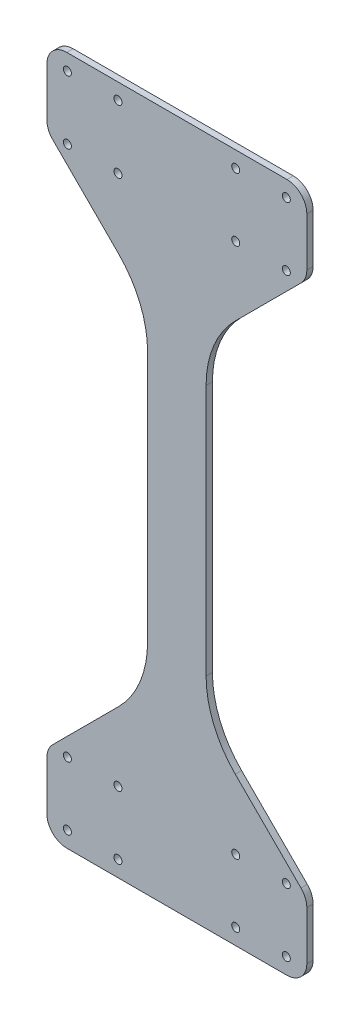
SolidWorks part; units mm, degrees
ref_plane "Front Plane" through (0, 0, 0) normal (0, 0, 1) x (1, 0, 0)
ref_plane "Top Plane" through (0, 0, 0) normal (0, 1, 0) x (1, 0, 0)
ref_plane "Right Plane" through (0, 0, 0) normal (1, 0, 0) x (0, 0, -1)
sketch "Sketch1" plane through (0, 0, 0) normal (0, 0, 1) x (1, 0, 0)
  line L0 (39.3854, -40.0501) -> (39.3854, -52.4111) construction
  line L1 (165.9345, -56.675) -> (165.9345, -42.05) construction
  line L2 (157.3152, -8.05) -> (165.9345, -16.6693)
  line L3 (157.3152, 245.3495) -> (165.9345, 253.9688)
  line L4 (39.3854, -40.0501) -> (39.3854, -52.4111)
  line L5 (165.9345, -56.675) -> (165.9345, -42.05)
  line L6 (165.9345, 245.3495) -> (39.3854, 245.3495)
  line L7 (165.9345, 279.3495) -> (165.9345, 245.3495)
  line L8 (39.3854, -52.4111) -> (165.9345, -56.675)
  line L9 (39.3854, 289.7105) -> (165.9345, 293.9745)
  line L10 (39.3854, -40.0501) -> (39.3854, -16.6693)
  line L11 (165.9345, -42.05) -> (165.9345, -16.6693)
  line L12 (157.3152, -8.05) -> (48.0047, -8.0501)
  line L13 (42.1433, 0) -> (42.1433, 237.2995) construction
  line L14 (42.1433, 118.6497) -> (215.0534, 118.6497) construction
  line L15 (165.9345, 293.9745) -> (165.9345, 279.3495)
  line L16 (39.3854, 277.3495) -> (39.3854, 245.3495)
  line L17 (39.3854, 277.3495) -> (39.3854, 289.7105)
  line L18 (102.66, -54.5431) -> (102.66, 291.8425) construction
  line L19 (102.66, 291.8425) -> (73.0854, -499321.8282) construction
  line L20 (39.3854, -16.6693) -> (89.96, 33.9052)
  line L21 (89.96, -8.05) -> (115.36, -8.05)
  line L22 (89.96, -8.05) -> (89.96, 245.3495)
  line L23 (89.96, 245.3495) -> (115.36, 245.3495)
  line L24 (115.36, -8.05) -> (115.36, 245.3495)
  line L25 (89.96, -8.05) -> (115.36, 245.3495) construction
  line L26 (89.96, 245.3495) -> (115.36, -8.05) construction
  line L27 (115.36, 33.9052) -> (157.3152, -8.05)
  line L28 (115.36, 203.3943) -> (157.3152, 245.3495)
  line L29 (39.3854, 253.9688) -> (89.96, 203.3943)
  arc A0 (157.6345, 249.9303) -> (157.6345, 253.9689) centre (157.6345, 251.9496) cw
  arc A1 (157.6345, 253.9689) -> (157.6345, 249.9303) centre (157.6345, 251.9496) cw
  arc A2 (73.0854, 249.9303) -> (73.0854, 253.9689) centre (73.0854, 251.9496) ccw
  arc A3 (73.0854, 253.9689) -> (73.0854, 249.9303) centre (73.0854, 251.9496) ccw
  arc A4 (73.0854, 249.9303) -> (73.0854, 253.9689) centre (73.0854, 251.9496) ccw
  arc A5 (73.0854, 253.9689) -> (73.0854, 249.9303) centre (73.0854, 251.9496) ccw
  arc A6 (47.6854, 249.9303) -> (47.6854, 253.9689) centre (47.6854, 251.9496) cw
  arc A7 (47.6854, 253.9689) -> (47.6854, 249.9303) centre (47.6854, 251.9496) cw
  arc A10 (47.6854, 281.6802) -> (47.6854, 285.7188) centre (47.6854, 283.6995) cw
  arc A11 (47.6854, 285.7188) -> (47.6854, 281.6802) centre (47.6854, 283.6995) cw
  arc A14 (157.6345, -48.4194) -> (157.6345, -44.3807) centre (157.6345, -46.4001) ccw
  arc A15 (157.6345, -44.3807) -> (157.6345, -48.4194) centre (157.6345, -46.4001) ccw
  arc A16 (157.6345, -48.4194) -> (157.6345, -44.3807) centre (157.6345, -46.4001) ccw
  arc A17 (157.6345, -44.3807) -> (157.6345, -48.4194) centre (157.6345, -46.4001) ccw
  arc A18 (73.0854, 281.6802) -> (73.0854, 285.7188) centre (73.0854, 283.6995) cw
  arc A19 (73.0854, 285.7188) -> (73.0854, 281.6802) centre (73.0854, 283.6995) cw
  arc A22 (157.6345, -16.6693) -> (157.6345, -12.6307) centre (157.6345, -14.65) ccw
  arc A23 (157.6345, -12.6307) -> (157.6345, -16.6693) centre (157.6345, -14.65) ccw
  arc A24 (157.6345, -16.6693) -> (157.6345, -12.6307) centre (157.6345, -14.65) ccw
  arc A25 (157.6345, -12.6307) -> (157.6345, -16.6693) centre (157.6345, -14.65) ccw
  arc A26 (73.0854, -16.6693) -> (73.0854, -12.6307) centre (73.0854, -14.65) ccw
  arc A27 (73.0854, -12.6307) -> (73.0854, -16.6693) centre (73.0854, -14.65) ccw
  arc A28 (73.0854, -16.6693) -> (73.0854, -12.6307) centre (73.0854, -14.65) ccw
  arc A29 (73.0854, -12.6307) -> (73.0854, -16.6693) centre (73.0854, -14.65) ccw
  arc A30 (73.0854, 249.9303) -> (73.0854, 253.9689) centre (73.0854, 251.9496) cw
  arc A31 (73.0854, 253.9689) -> (73.0854, 249.9303) centre (73.0854, 251.9496) cw
  arc A34 (157.6345, 249.9303) -> (157.6345, 253.9689) centre (157.6345, 251.9496) ccw
  arc A35 (157.6345, 253.9689) -> (157.6345, 249.9303) centre (157.6345, 251.9496) ccw
  arc A36 (157.6345, 249.9303) -> (157.6345, 253.9689) centre (157.6345, 251.9496) ccw
  arc A37 (157.6345, 253.9689) -> (157.6345, 249.9303) centre (157.6345, 251.9496) ccw
  arc A38 (47.6854, 249.9303) -> (47.6854, 253.9689) centre (47.6854, 251.9496) ccw
  arc A39 (47.6854, 253.9689) -> (47.6854, 249.9303) centre (47.6854, 251.9496) ccw
  arc A40 (47.6854, 249.9303) -> (47.6854, 253.9689) centre (47.6854, 251.9496) ccw
  arc A41 (47.6854, 253.9689) -> (47.6854, 249.9303) centre (47.6854, 251.9496) ccw
  arc A42 (73.0854, -48.4194) -> (73.0854, -44.3807) centre (73.0854, -46.4001) ccw
  arc A43 (73.0854, -44.3807) -> (73.0854, -48.4194) centre (73.0854, -46.4001) ccw
  arc A44 (73.0854, -48.4194) -> (73.0854, -44.3807) centre (73.0854, -46.4001) ccw
  arc A45 (73.0854, -44.3807) -> (73.0854, -48.4194) centre (73.0854, -46.4001) ccw
  arc A46 (132.2345, 249.9303) -> (132.2345, 253.9689) centre (132.2345, 251.9496) ccw
  arc A47 (132.2345, 253.9689) -> (132.2345, 249.9303) centre (132.2345, 251.9496) ccw
  arc A48 (132.2345, 249.9303) -> (132.2345, 253.9689) centre (132.2345, 251.9496) ccw
  arc A49 (132.2345, 253.9689) -> (132.2345, 249.9303) centre (132.2345, 251.9496) ccw
  arc A50 (47.6854, -48.4194) -> (47.6854, -44.3808) centre (47.6854, -46.4001) ccw
  arc A51 (47.6854, -44.3808) -> (47.6854, -48.4194) centre (47.6854, -46.4001) ccw
  arc A52 (47.6854, -48.4194) -> (47.6854, -44.3808) centre (47.6854, -46.4001) ccw
  arc A53 (47.6854, -44.3808) -> (47.6854, -48.4194) centre (47.6854, -46.4001) ccw
  arc A54 (47.6854, -16.6693) -> (47.6854, -12.6307) centre (47.6854, -14.65) ccw
  arc A55 (47.6854, -12.6307) -> (47.6854, -16.6693) centre (47.6854, -14.65) ccw
  arc A56 (47.6854, -16.6693) -> (47.6854, -12.6307) centre (47.6854, -14.65) ccw
  arc A57 (47.6854, -12.6307) -> (47.6854, -16.6693) centre (47.6854, -14.65) ccw
  arc A58 (157.6345, 281.6802) -> (157.6345, 285.7188) centre (157.6345, 283.6995) cw
  arc A59 (157.6345, 285.7188) -> (157.6345, 281.6802) centre (157.6345, 283.6995) cw
  arc A62 (132.2345, -16.6693) -> (132.2345, -12.6307) centre (132.2345, -14.65) ccw
  arc A63 (132.2345, -12.6307) -> (132.2345, -16.6693) centre (132.2345, -14.65) ccw
  arc A64 (132.2345, -16.6693) -> (132.2345, -12.6307) centre (132.2345, -14.65) ccw
  arc A65 (132.2345, -12.6307) -> (132.2345, -16.6693) centre (132.2345, -14.65) ccw
  arc A66 (132.2345, -48.4194) -> (132.2345, -44.3808) centre (132.2345, -46.4001) ccw
  arc A67 (132.2345, -44.3808) -> (132.2345, -48.4194) centre (132.2345, -46.4001) ccw
  arc A68 (132.2345, -48.4194) -> (132.2345, -44.3808) centre (132.2345, -46.4001) ccw
  arc A69 (132.2345, -44.3808) -> (132.2345, -48.4194) centre (132.2345, -46.4001) ccw
  point P62 (102.66, 118.6497)
  dimension "D3" = 0
  dimension "D2" = 25.4
  dimension "D1" = 0
  dimension "D4" = 0
  dimension "D5" = 0
  dimension "D6" = 0
  dimension "D7" = 0
  dimension "D9" = 0
  dimension "D10" = 0
  dimension "D11" = 0
  dimension "D12" = 0
  dimension "D13" = 0
  dimension "D14" = 0
extrude "Boss-Extrude1" add sketch "Sketch1" along normal blind 3.175 contours L20 L10 L4 L8 L5 L11 L2 L12 A69 A68 A65 A64 A57 A56 A53 A52 A45 A44 A29 A28 A25 A24 A17 A16 | L27 L24 L12 | L12 L24 L6 L22 | L12 L22 L20 | L16 L29 L6 L3 L7 L15 L9 L17 A49 A48 A5 A4 A0 A1 A6 A7 A10 A11 A18 A19 A58 A59 | L24 L28 L6 | L6 L29 L22
sketch "Sketch2" plane through (0, 0, 3.175) normal (0, 0, 1) x (1, 0, 0)
  line L0 (165.9345, -56.675) -> (165.9345, -16.6693) construction
  line L1 (39.3854, -52.4111) -> (84.3854, -52.4111)
  line L2 (39.3854, -52.4111) -> (39.3854, -7.4111)
  line L3 (39.3854, -7.4111) -> (84.3854, -7.4111)
  line L4 (84.3854, -52.4111) -> (84.3854, -7.4111)
  line L5 (165.9345, -52.4111) -> (120.9345, -52.4111)
  line L6 (165.9345, -52.4111) -> (165.9345, -7.4111)
  line L7 (165.9345, -7.4111) -> (120.9345, -7.4111)
  line L8 (120.9345, -52.4111) -> (120.9345, -7.4111)
  line L9 (89.96, 118.6497) -> (115.36, 118.6497) construction
  line L10 (89.96, 33.9052) -> (89.96, 203.3943) construction
  line L11 (115.36, 33.9052) -> (115.36, 203.3943) construction
  line L12 (165.9345, 289.7105) -> (120.9345, 289.7105)
  line L13 (39.3854, 289.7105) -> (84.3854, 289.7105)
  line L14 (84.3854, -52.4111) -> (120.9345, -52.4111)
  line L15 (84.3854, 289.7105) -> (120.9345, 289.7105)
  line M9 (39.3854, -52.4111) -> (165.9345, -56.675)
  line M10 (165.9345, -56.675) -> (165.9345, -16.6693)
  line M14 (165.9345, 253.9688) -> (165.9345, 293.9745)
  line M15 (165.9345, 293.9745) -> (39.3854, 289.7105)
  dimension "D1" = 45
extrude "Cut-Extrude1" cut sketch "Sketch2" against normal blind 10 contours L14 L1 L5 M9 M10 | L13 L15 L12 M14 M15
sketch "Sketch3" plane through (0, 0, 3.175) normal (0, 0, 1) x (1, 0, 0)
  line L25 (37.3854, -15.8409) -> (37.3854, -54.4111)
  line L26 (37.3854, -54.4111) -> (167.9345, -54.4111)
  line L27 (167.9345, -54.4111) -> (167.9345, -15.8409)
  line L28 (167.9345, -15.8409) -> (117.36, 34.7337)
  line L29 (117.36, 34.7337) -> (117.36, 202.5658)
  line L30 (117.36, 202.5658) -> (167.9345, 253.1404)
  line L31 (167.9345, 253.1404) -> (167.9345, 291.7105)
  line L32 (167.9345, 291.7105) -> (37.3854, 291.7105)
  line L33 (37.3854, 291.7105) -> (37.3854, 253.1404)
  line L34 (37.3854, 253.1404) -> (87.96, 202.5658)
  line L35 (87.96, 202.5658) -> (87.96, 34.7337)
  line L36 (87.96, 34.7337) -> (37.3854, -15.8409)
  line L37 (37.3854, -15.8409) -> (37.3854, -54.4111)
  line L38 (37.3854, -54.4111) -> (167.9345, -54.4111)
  line L39 (167.9345, -54.4111) -> (167.9345, -15.8409)
  line L40 (167.9345, -15.8409) -> (117.36, 34.7337)
  line L41 (117.36, 34.7337) -> (117.36, 202.5658)
  line L42 (117.36, 202.5658) -> (167.9345, 253.1404)
  line L43 (167.9345, 253.1404) -> (167.9345, 291.7105)
  line L44 (167.9345, 291.7105) -> (37.3854, 291.7105)
  line L45 (37.3854, 291.7105) -> (37.3854, 253.1404)
  line L46 (37.3854, 253.1404) -> (87.96, 202.5658)
  line L47 (87.96, 202.5658) -> (87.96, 34.7337)
  line L48 (87.96, 34.7337) -> (37.3854, -15.8409)
  circle A1 centre (132.2345, -46.4001) radius 2.0193
  circle A2 centre (132.2345, -46.4001) radius 2.0193
  circle A3 centre (132.2345, -14.65) radius 2.0193
  circle A4 centre (132.2345, -14.65) radius 2.0193
  circle A5 centre (47.6854, -14.65) radius 2.0193
  circle A6 centre (47.6854, -14.65) radius 2.0193
  circle A7 centre (47.6854, -46.4001) radius 2.0193
  circle A8 centre (47.6854, -46.4001) radius 2.0193
  circle A9 centre (73.0854, -46.4001) radius 2.0193
  circle A10 centre (73.0854, -46.4001) radius 2.0193
  circle A11 centre (73.0854, -14.65) radius 2.0193
  circle A12 centre (73.0854, -14.65) radius 2.0193
  circle A13 centre (157.6345, -14.65) radius 2.0193
  circle A14 centre (157.6345, -14.65) radius 2.0193
  circle A15 centre (157.6345, -46.4001) radius 2.0193
  circle A16 centre (157.6345, -46.4001) radius 2.0193
  circle A17 centre (132.2345, 251.9496) radius 2.0193
  circle A18 centre (132.2345, 251.9496) radius 2.0193
  circle A19 centre (73.0854, 251.9496) radius 2.0193
  circle A20 centre (73.0854, 251.9496) radius 2.0193
  circle A21 centre (157.6345, 251.9496) radius 2.0193
  circle A22 centre (157.6345, 251.9496) radius 2.0193
  circle A23 centre (47.6854, 251.9496) radius 2.0193
  circle A24 centre (47.6854, 251.9496) radius 2.0193
  circle A25 centre (47.6854, 283.6995) radius 2.0193
  circle A26 centre (47.6854, 283.6995) radius 2.0193
  circle A27 centre (73.0854, 283.6995) radius 2.0193
  circle A28 centre (73.0854, 283.6995) radius 2.0193
  circle A29 centre (157.6345, 283.6995) radius 2.0193
  circle A30 centre (157.6345, 283.6995) radius 2.0193
  dimension "D1" = 2
  dimension "D2" = 0
  dimension "D3" = 0
  dimension "D4" = 0
  dimension "D5" = 0
  dimension "D6" = 0
  dimension "D7" = 0
  dimension "D8" = 0
  dimension "D9" = 0
  dimension "D10" = 0
  dimension "D11" = 0
  dimension "D12" = 0
  dimension "D13" = 0
  dimension "D14" = 0
  dimension "D15" = 0
  dimension "D16" = 0
extrude "Boss-Extrude2" add sketch "Sketch3" against normal up to surface (3.175 mm away) up to face at (159.6538, 283.6995, 0)
fillet "Fillet1" radius 10 8 edges at (37.3854, 253.1404, 1.5875) (37.3854, 291.7105, 1.5875) (167.9345, 291.7105, 1.5875) (167.9345, 253.1404, 1.5875) (37.3854, -15.8409, 1.5875) (167.9345, -15.8409, 1.5875) (167.9345, -54.4111, 1.5875) (37.3854, -54.4111, 1.5875)
fillet "Fillet2" radius 50 4 edges at (87.96, 34.7337, 1.5875) (117.36, 34.7337, 1.5875) (87.96, 202.5658, 1.5875) (117.36, 202.5658, 1.5875)
sketch "Sketch4" plane through (0, 0, 3.175) normal (0, 0, 1) x (1, 0, 0)
  circle A0 centre (132.2345, 283.6995) radius 2.02
  dimension "D1" = 4.04
extrude "Cut-Extrude2" cut sketch "Sketch4" against normal blind 10
